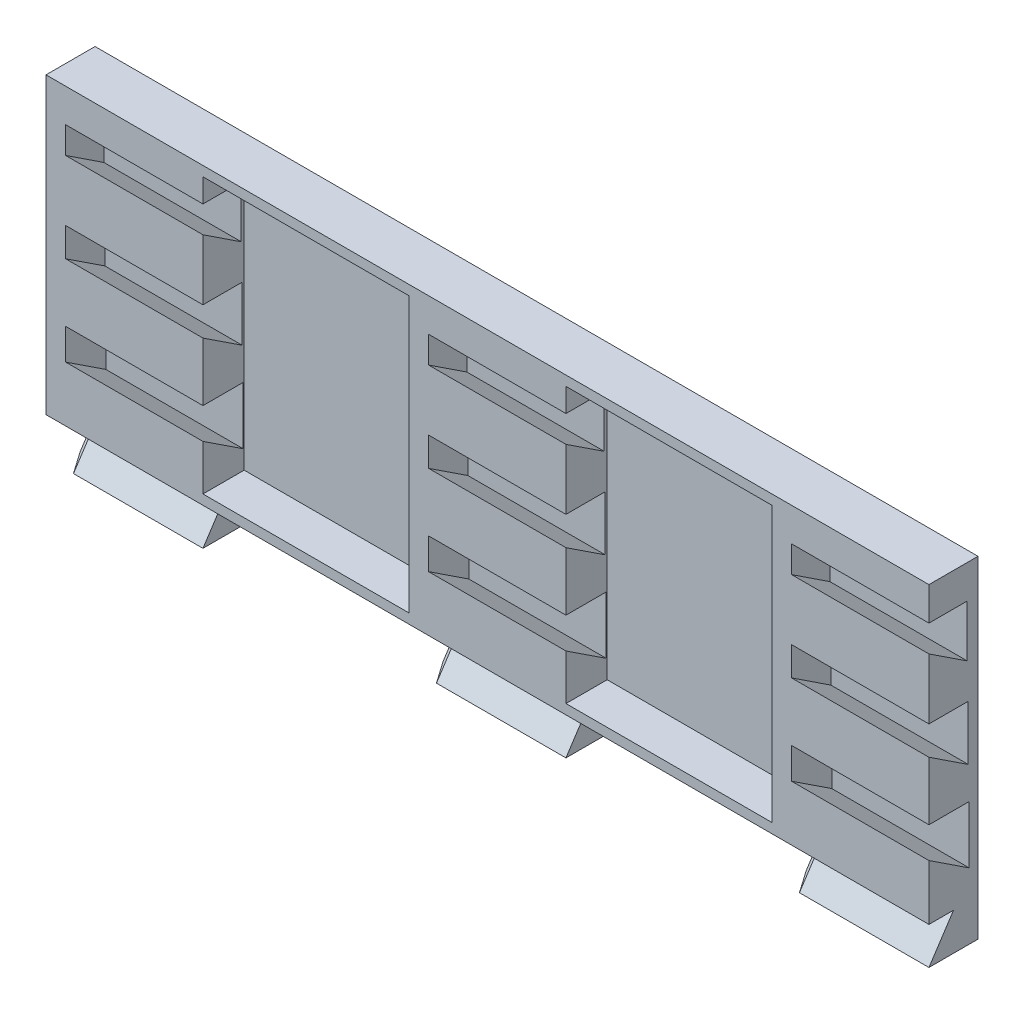
SolidWorks part; units mm, degrees
material "ABS"
ref_plane "Front Plane" through (0, 0, 0) normal (0, 0, 1) x (1, 0, 0)
ref_plane "Top Plane" through (0, 0, 0) normal (0, 1, 0) x (1, 0, 0)
ref_plane "Right Plane" through (0, 0, 0) normal (1, 0, 0) x (0, 0, -1)
sketch "Sketch1" plane through (0, 0, 0) normal (0, 0, 1) x (1, 0, 0)
  line L1 (-74.93, -7.9375) -> (74.93, -7.9375)
  line L2 (-74.93, -7.9375) -> (-74.93, 7.9375)
  line L3 (-74.93, 7.9375) -> (74.93, 7.9375)
  line L4 (74.93, -7.9375) -> (74.93, 7.9375)
  line L5 (-74.93, -7.9375) -> (74.93, 7.9375) construction
  line L6 (-74.93, 7.9375) -> (74.93, -7.9375) construction
  point P0 (0, 0)
  dimension "D1" = 15.875
  dimension "D2" = 149.86
sketch "Sketch2" plane through (0, 0, 0) normal (1, 0, 0) x (0, 0, -1)
  line L0 (0, -19.05) -> (-3.175, -23.876)
  line L1 (-3.175, -19.05) -> (0, -19.05)
  line L2 (-3.175, -19.05) -> (-3.175, 19.05)
  line L3 (-3.175, 19.05) -> (3.175, 19.05)
  line L4 (3.175, -19.05) -> (3.175, 19.05)
  line L5 (-3.175, -19.05) -> (3.175, 19.05) construction
  line L6 (-3.175, 19.05) -> (3.175, -19.05) construction
  line L7 (-3.175, -23.876) -> (3.175, -23.876)
  line L8 (3.175, -23.876) -> (3.175, -19.05)
  point P0 (0, 0)
  dimension "D1" = 6.35
  dimension "D2" = 38.1
  dimension "D3" = 4.826
extrude "Boss-Extrude1" add sketch "Sketch2" along normal blind 114.3
sketch "Sketch4" plane through (114.3, 0, 0) normal (1, 0, 0) x (0, 0, -1)
  line L0 (-3.175, -11.43) -> (3.175, -11.43) construction
  line L1 (-3.175, 19.05) -> (-3.175, -19.05) construction
  line L2 (3.175, -23.876) -> (3.175, 19.05) construction
  line L3 (-3.175, 0) -> (3.175, 0) construction
  line L4 (-3.175, 11.43) -> (3.175, 11.43) construction
  line L5 (-3.175, 11.43) -> (1.651, 8.255) construction
  line L6 (1.651, 8.255) -> (1.651, 14.605) construction
  line L7 (1.651, 14.605) -> (-3.175, 14.605) construction
  line L8 (-3.175, 14.732) -> (-3.175, 11.278)
  line L9 (-3.175, 11.278) -> (1.778, 8.0194)
  line L10 (1.778, 8.0194) -> (1.778, 14.732)
  line L11 (1.778, 14.732) -> (-3.175, 14.732)
  line L12 (0.2806, 14.732) -> (0.2806, 14.605) construction
  line L13 (1.651, 12.3255) -> (1.778, 12.3255) construction
  line L14 (-1.0609, 10.0392) -> (-1.1307, 9.9331) construction
  line L15 (-3.175, 0) -> (1.651, -3.175) construction
  line L16 (1.651, -3.175) -> (1.651, 3.175) construction
  line L17 (1.651, 3.175) -> (-3.175, 3.175) construction
  line L18 (-3.175, -11.43) -> (1.651, -14.605) construction
  line L19 (1.651, -14.605) -> (1.651, -8.255) construction
  line L20 (1.651, -8.255) -> (-3.175, -8.255) construction
  line L21 (-3.175, 3.429) -> (-3.175, -0.304)
  line L22 (-3.175, -0.304) -> (1.905, -3.6461)
  line L23 (1.905, -3.6461) -> (1.905, 3.429)
  line L24 (1.905, 3.429) -> (-3.175, 3.429)
  line L25 (-3.175, -7.874) -> (2.032, -7.874)
  line L26 (2.032, -7.874) -> (2.032, -15.3117)
  line L27 (2.032, -15.3117) -> (-3.175, -11.8861)
  line L28 (-3.175, -11.8861) -> (-3.175, -7.874)
  line L29 (0.8637, -14.087) -> (0.6543, -14.4053) construction
  line L30 (1.651, -12.9747) -> (2.032, -12.9747) construction
  line L31 (0.5519, -8.255) -> (0.5519, -7.874) construction
  line L32 (-1.4258, -1.1508) -> (-1.5654, -1.363) construction
  line L33 (1.651, -1.1508) -> (1.905, -1.1508) construction
  line L34 (0.4322, 3.175) -> (0.4322, 3.429) construction
  point P13 (1.651, 11.43)
  point P25 (1.651, 0)
  point P32 (1.651, -11.43)
  dimension "D1" = 11.43
  dimension "D2" = 11.43
  dimension "D3" = 6.35
  dimension "D4" = 4.826
  dimension "D5" = 0.127
  dimension "D6" = 0.254
  dimension "D7" = 0.381
extrude "Cut-Extrude2" cut sketch "Sketch4" against normal blind 17.78
pattern_linear "LPattern2" count 3 spacing 46.99 along (-1, 0, 0) of "Cut-Extrude2"
sketch "Sketch5" plane through (0, 0, 3.175) normal (0, 0, 1) x (1, 0, 0)
  line L0 (67.31, -3.6461) -> (67.31, 3.429) construction
  line L1 (67.31, 17.78) -> (93.98, 17.78)
  line L2 (67.31, 17.78) -> (67.31, -17.78)
  line L3 (67.31, -17.78) -> (93.98, -17.78)
  line L4 (93.98, 17.78) -> (93.98, -17.78)
  line L5 (96.52, 8.0194) -> (96.52, 14.732) construction
  line L6 (114.3, 19.05) -> (0, 19.05) construction
  line L7 (114.3, -19.05) -> (0, -19.05) construction
  line L9 (20.32, 17.78) -> (46.99, 17.78)
  line L10 (20.32, 17.78) -> (20.32, -17.78)
  line L11 (20.32, -17.78) -> (46.99, -17.78)
  line L12 (46.99, 17.78) -> (46.99, -17.78)
  line L14 (20.32, 3.429) -> (20.32, -0.304) construction
  dimension "D1" = 2.54
  dimension "D2" = 1.27
  dimension "D3" = 1.27
extrude "Cut-Extrude3" cut sketch "Sketch5" against normal blind 5.334
sketch "Sketch6" plane through (0, 0, 3.175) normal (0, 0, 1) x (1, 0, 0)
  line L0 (114.3, -23.876) -> (0, -23.876) construction
  line L1 (0, -19.05) -> (2.54, -19.05)
  line L2 (0, -19.05) -> (0, -23.876)
  line L3 (0, -23.876) -> (2.54, -23.876)
  line L4 (2.54, -19.05) -> (2.54, -23.876)
  line L5 (114.3, -19.05) -> (0, -19.05) construction
  line L6 (20.32, -19.05) -> (49.53, -19.05)
  line L7 (20.32, -19.05) -> (20.32, -23.876)
  line L8 (20.32, -23.876) -> (49.53, -23.876)
  line L9 (49.53, -19.05) -> (49.53, -23.876)
  line L10 (96.52, -7.874) -> (96.52, -11.8861) construction
  line L11 (67.31, -19.05) -> (96.52, -19.05)
  line L12 (67.31, -19.05) -> (67.31, -23.876)
  line L13 (67.31, -23.876) -> (96.52, -23.876)
  line L14 (96.52, -19.05) -> (96.52, -23.876)
  line L15 (67.31, 17.78) -> (67.31, -17.78) construction
  line L16 (49.53, -7.874) -> (49.53, -11.8861) construction
  line L17 (20.32, -11.8861) -> (20.32, -17.78) construction
  line L18 (2.54, -7.874) -> (2.54, -11.8861) construction
extrude "Cut-Extrude4" cut sketch "Sketch6" against normal through all
chamfer "Chamfer1" distance 1.016 angle 45 9 edges at (2.54, -21.463, -3.175) (2.54, -23.876, 0) (2.54, -21.463, 1.5875) (96.52, -21.463, -3.175) (96.52, -23.876, 0) (96.52, -21.463, 1.5875) (49.53, -21.463, -3.175) (49.53, -23.876, 0) (49.53, -21.463, 1.5875)
